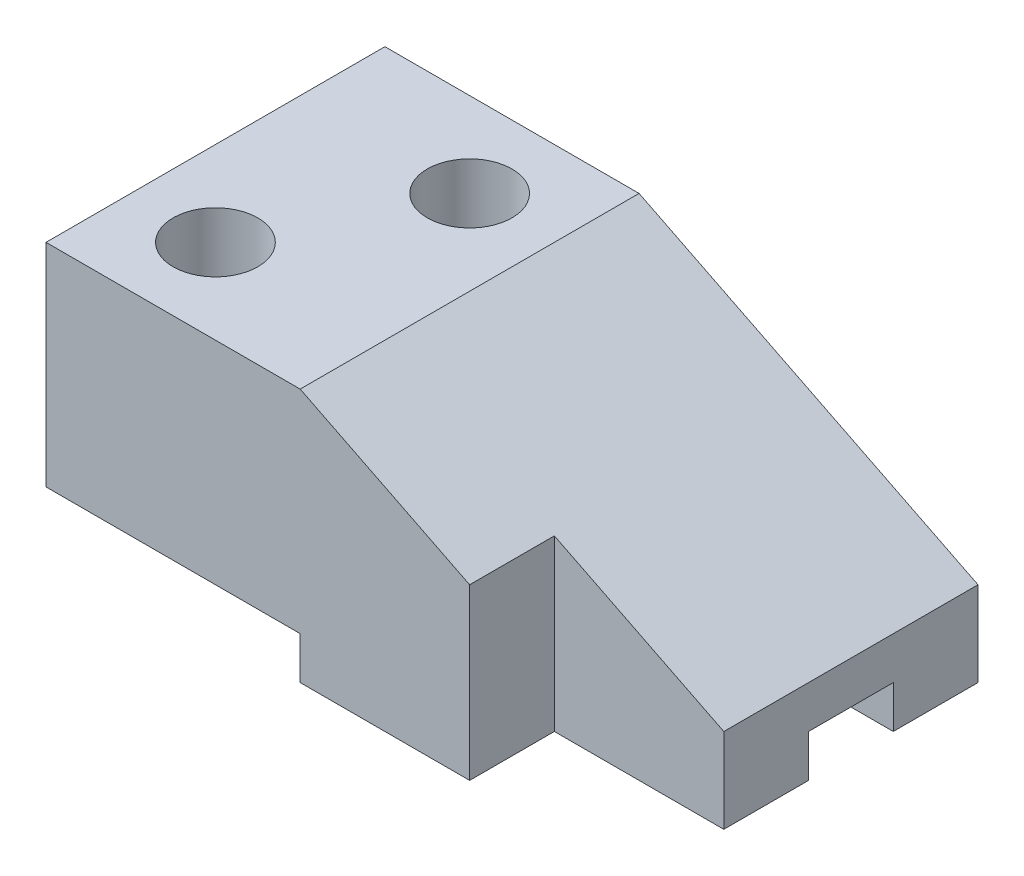
SolidWorks part; units mm, degrees
ref_plane "Front Plane" through (0, 0, 0) normal (0, 0, 1) x (1, 0, 0)
ref_plane "Top Plane" through (0, 0, 0) normal (0, 1, 0) x (1, 0, 0)
ref_plane "Right Plane" through (0, 0, 0) normal (1, 0, 0) x (0, 0, -1)
sketch "Sketch2" plane through (0, 0, 0) normal (0, 1, 0) x (1, 0, 0)
  line L1 (0, 0) -> (70, 0)
  line L2 (0, 0) -> (0, 40)
  line L3 (0, 40) -> (70, 40)
  line L4 (70, 0) -> (70, 40)
  dimension "D1" = 70
  dimension "D2" = 40
extrude "Boss-Extrude1" add sketch "Sketch2" along normal blind 30
sketch "Sketch4" plane through (0, 0, 0) normal (0, 0, 1) x (1, 0, 0)
  line L0 (70, 30) -> (30, 30)
  line L1 (0, 30) -> (70, 30) construction
  line L2 (30, 30) -> (70, 10)
  line L3 (70, 30) -> (70, 0) construction
  line L4 (70, 10) -> (70, 30)
  dimension "D1" = 40
  dimension "D2" = 20
extrude "Cut-Extrude2" cut sketch "Sketch4" against normal blind 49 contours L4 L0 L2
sketch "Sketch5" plane through (0, 0, 0) normal (0, -1, 0) x (-1, 0, 0)
  line L1 (-70, 0) -> (-50, 0)
  line L2 (-70, 0) -> (-70, 10)
  line L3 (-70, 10) -> (-50, 10)
  line L4 (-50, 0) -> (-50, 10)
  dimension "D1" = 10
  dimension "D2" = 20
extrude "Cut-Extrude3" cut sketch "Sketch5" against normal blind 49
sketch "Sketch6" plane through (0, 0, 0) normal (-1, 0, 0) x (0, 0, 1)
  line L0 (-40, 30) -> (-40, 0) construction
  line L1 (0, 0) -> (-40, 0)
  line L2 (0, 0) -> (0, 5)
  line L3 (0, 5) -> (-40, 5)
  line L4 (-40, 0) -> (-40, 5)
  dimension "D1" = 5
extrude "Cut-Extrude4" cut sketch "Sketch6" against normal blind 30
sketch "Sketch7" plane through (30, 0, 0) normal (-1, 0, 0) x (0, 0, 1)
  line L0 (-10, 0) -> (-20, 0) construction
  line L1 (-10, 0) -> (-40, 0) construction
  line L3 (-20, 0) -> (-30, 0)
  line L4 (-20, 0) -> (-20, 5)
  line L5 (-20, 5) -> (-30, 5)
  line L6 (-30, 0) -> (-30, 5)
  dimension "D1" = 10
  dimension "D2" = 10
  dimension "D3" = 5
extrude "Cut-Extrude5" cut sketch "Sketch7" against normal through all contours L4 L3 L6 L5
sketch "Sketch8" plane through (0, 30, 0) normal (0, 1, 0) x (1, 0, 0)
  line L0 (0, 0) -> (10, 0) construction
  line L1 (0, 0) -> (30, 0) construction
  line L2 (10, 0) -> (10, 10) construction
  circle A0 centre (10, 10) radius 5
  dimension "D3" = 10
  dimension "D1" = 10
  dimension "D2" = 10
extrude "Cut-Extrude6" cut sketch "Sketch8" against normal through all contours A0
sketch "Sketch9" plane through (0, 30, 0) normal (0, 1, 0) x (1, 0, 0)
  line L0 (30, 40) -> (20, 40) construction
  line L1 (30, 40) -> (0, 40) construction
  line L2 (20, 40) -> (20, 30) construction
  circle A0 centre (20, 30) radius 5
  dimension "D3" = 10
  dimension "D1" = 10
  dimension "D2" = 10
extrude "Cut-Extrude7" cut sketch "Sketch9" against normal through all contours A0
